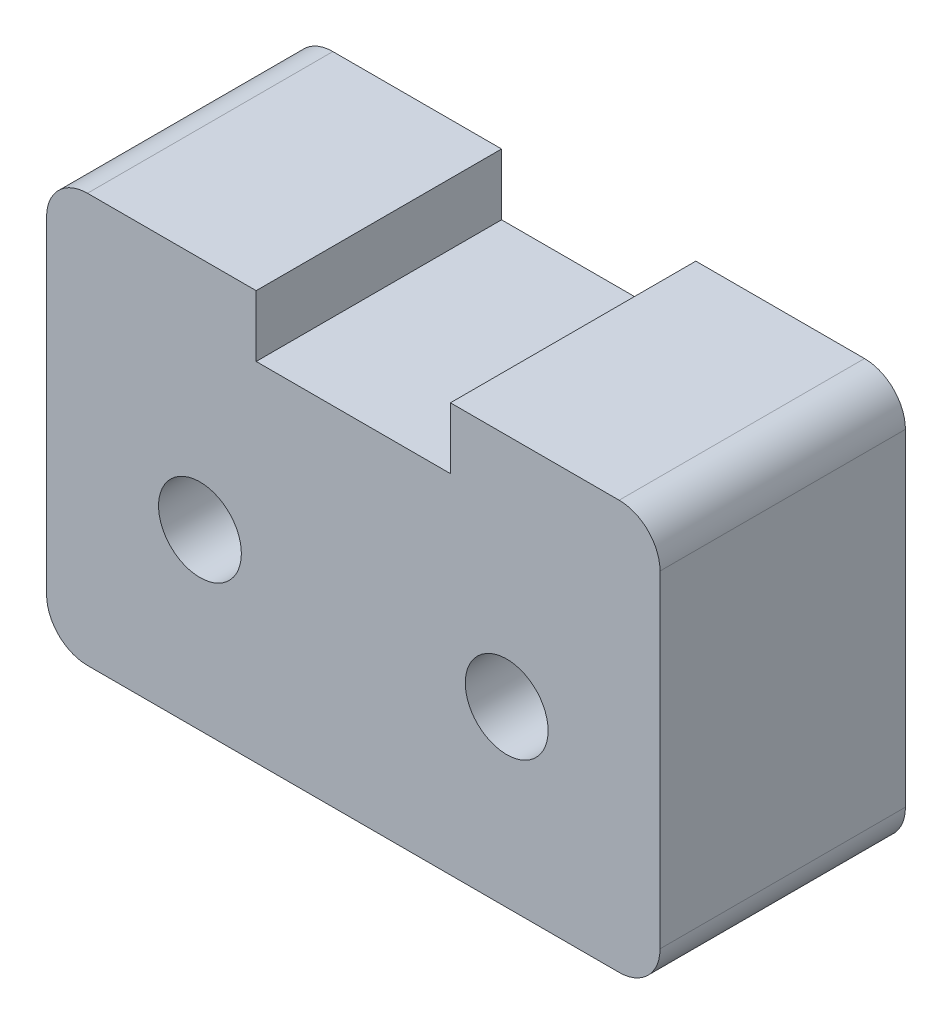
SolidWorks part; units mm, degrees
material "ABS"
ref_plane "前视基准面" through (0, 0, 0) normal (0, 0, 1) x (1, 0, 0)
ref_plane "上视基准面" through (0, 0, 0) normal (0, 1, 0) x (1, 0, 0)
ref_plane "右视基准面" through (0, 0, 0) normal (1, 0, 0) x (0, 0, -1)
other "Configuration Table"
sketch "草图1" plane through (0, 0, 0) normal (0, 0, 1) x (1, 0, 0)
  line L0 (4.75, 0) -> (-4.75, 0)
  line L1 (-4.75, 0) -> (-4.75, 3)
  line L2 (-4.75, 3) -> (-15, 3)
  line L3 (-15, 3) -> (-15, -17)
  line L4 (-15, -17) -> (15, -17)
  line L5 (0, -17) -> (0, 0) construction
  line L6 (15, 3) -> (15, -17)
  line L7 (4.75, 3) -> (15, 3)
  line L8 (4.75, 0) -> (4.75, 3)
  dimension "D1" = 30
  dimension "D2" = 3
  dimension "D3" = 9.5
  dimension "D4" = 20
extrude "凸台-拉伸1" add sketch "草图1" along normal blind 12
fillet "圆角1" radius 2 4 edges at (15, -17, 6) (-15, -17, 6) (15, 3, 6) (-15, 3, 6)
sketch "草图2" plane through (0, 0, 12) normal (0, 0, 1) x (1, 0, 0)
  line L0 (0, 0) -> (0, -17) construction
  line L1 (-13, -17) -> (13, -17) construction
  circle A0 centre (-7.5, -8.5) radius 2.025
  circle A1 centre (7.5, -8.5) radius 2.025
  point P9 (0, -8.5)
  dimension "D1" = 4.05
  dimension "D2" = 15
extrude "切除-拉伸1" cut sketch "草图2" against normal through all both and the other way through all
